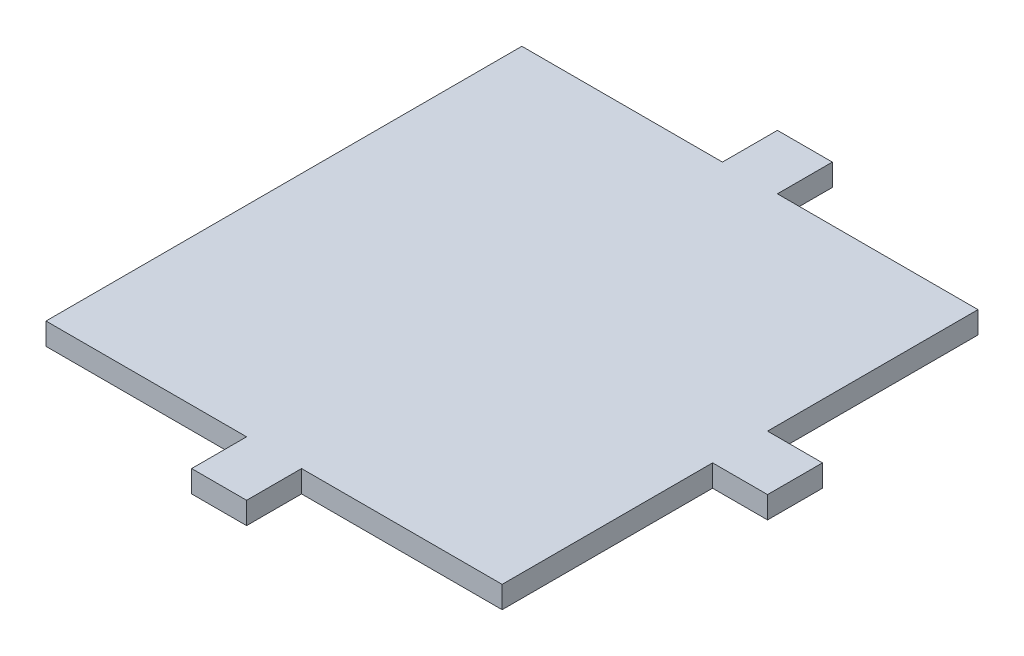
SolidWorks part; units mm, degrees
ref_plane "Front Plane" through (0, 0, 0) normal (0, 0, 1) x (1, 0, 0)
ref_plane "Top Plane" through (0, 0, 0) normal (0, 1, 0) x (1, 0, 0)
ref_plane "Right Plane" through (0, 0, 0) normal (1, 0, 0) x (0, 0, -1)
sketch "Sketch1" plane through (0, 0, 0) normal (0, 1, 0) x (1, 0, 0)
  line L5 (-3.5, -3.5) -> (3.5, -3.5)
  line L6 (-3.5, -3.5) -> (-3.5, 3.5)
  line L7 (-3.5, 3.5) -> (3.5, 3.5)
  line L8 (3.5, -3.5) -> (3.5, 3.5)
  line L9 (-3.5, -3.5) -> (3.5, 3.5) construction
  line L10 (-3.5, 3.5) -> (3.5, -3.5) construction
  point P0 (0, 0)
extrude "Boss-Extrude1" add sketch "Sketch1" along normal blind 3
sketch "Sketch3" plane through (0, 3, 0) normal (0, 1, 0) x (1, 0, 0)
  line L1 (-5, -5) -> (5, -5)
  line L2 (-5, -5) -> (-5, 5)
  line L3 (-5, 5) -> (5, 5)
  line L4 (5, -5) -> (5, 5)
  line L5 (-5, -5) -> (5, 5) construction
  line L6 (-5, 5) -> (5, -5) construction
  point P0 (0, 0)
extrude "Boss-Extrude2" add sketch "Sketch3" along normal blind 15
sketch "Sketch4" plane through (0, 18, 0) normal (0, 1, 0) x (1, 0, 0)
  line L0 (0, 0) -> (5.8574, 0) construction
  line L5 (10.8574, 43.2945) -> (10.8574, 53.2945)
  line L10 (-35.6426, 43.2945) -> (-35.6426, -43.2945)
  line L11 (47.3574, 43.2945) -> (-35.6426, -43.2945) construction
  line L12 (47.3574, -43.2945) -> (-35.6426, 43.2945) construction
  line L13 (0.8574, -43.2945) -> (0.8574, -53.2945)
  line L14 (0.8574, -53.2945) -> (10.8574, -53.2945)
  line L15 (10.8574, -43.2945) -> (10.8574, -53.2945)
  line L16 (47.3574, 5) -> (47.3574, 43.2945)
  line L17 (47.3574, 43.2945) -> (10.8574, 43.2945)
  line L18 (10.8574, 53.2945) -> (0.8574, 53.2945)
  line L19 (0.8574, 53.2945) -> (0.8574, 43.2945)
  line L20 (0.8574, 43.2945) -> (-35.6426, 43.2945)
  line L21 (47.3574, 5) -> (57.3574, 5)
  line L23 (47.3574, -5) -> (57.3574, -5)
  line L24 (57.3574, 5) -> (57.3574, -5)
  line L25 (47.3574, -5) -> (47.3574, -43.2945)
  line L26 (47.3574, -43.2945) -> (10.8574, -43.2945)
  line L27 (0.8574, -43.2945) -> (-35.6426, -43.2945)
  point P0 (0, 0)
  point P8 (5.8574, -43.2945)
  point P17 (47.3574, 0)
extrude "Boss-Extrude4" add sketch "Sketch4" along normal blind 4
